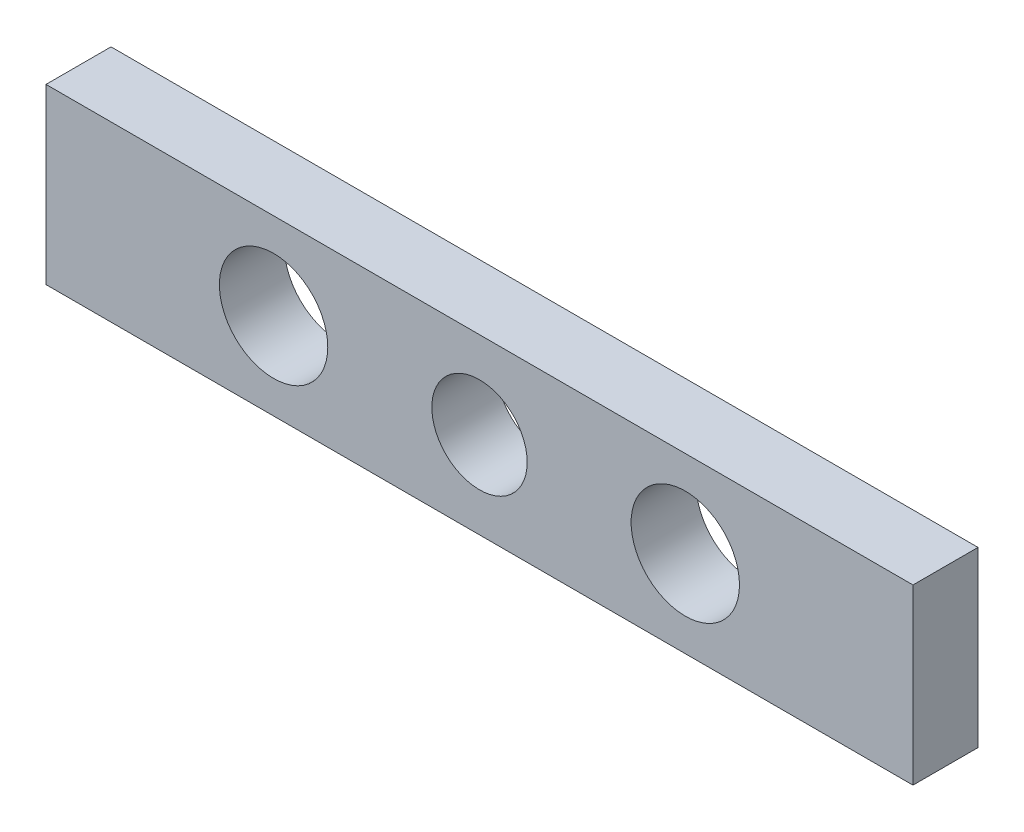
SolidWorks part; units mm, degrees
ref_plane "Front Plane" through (0, 0, 0) normal (0, 0, 1) x (1, 0, 0)
ref_plane "Top Plane" through (0, 0, 0) normal (0, 1, 0) x (1, 0, 0)
ref_plane "Right Plane" through (0, 0, 0) normal (1, 0, 0) x (0, 0, -1)
sketch "Sketch1" plane through (0, 0, 0) normal (0, 0, 1) x (1, 0, 0)
  line L1 (20.0023, 5) -> (-19.9977, 5)
  line L2 (20.0023, 5) -> (20.0023, -3)
  line L3 (20.0023, -3) -> (-19.9977, -3)
  line L4 (-19.9977, 5) -> (-19.9977, -3)
  line L5 (-19.9977, -3) -> (20.0023, -3)
  line L6 (-9.4977, 1) -> (9.4977, 1) construction
  circle A0 centre (0.0023, 1) radius 2.2
  arc A3 (11.9852, 1.25) -> (11.9852, 0.75) centre (9.4977, 1) ccw
  arc A4 (-11.9852, 0.75) -> (-11.9852, 1.25) centre (-9.4977, 1) ccw
  arc A5 (-11.9852, 1.25) -> (-11.9852, 0.75) centre (-9.4977, 1) ccw
  arc A6 (11.9852, 1.25) -> (11.9852, 0.75) centre (9.4977, 1) cw
  dimension "D1" = 4.4
  dimension "D2" = 18.9955
  dimension "D5" = 0
  dimension "D7" = 9.5
  dimension "D8" = 20
  dimension "D3" = 8
  dimension "D4" = 4
  dimension "D6" = 40
extrude "Boss-Extrude1" add sketch "Sketch1" along normal blind 3 contours L1 L4 L3 L2 A0 A5 A4 A3 A6
